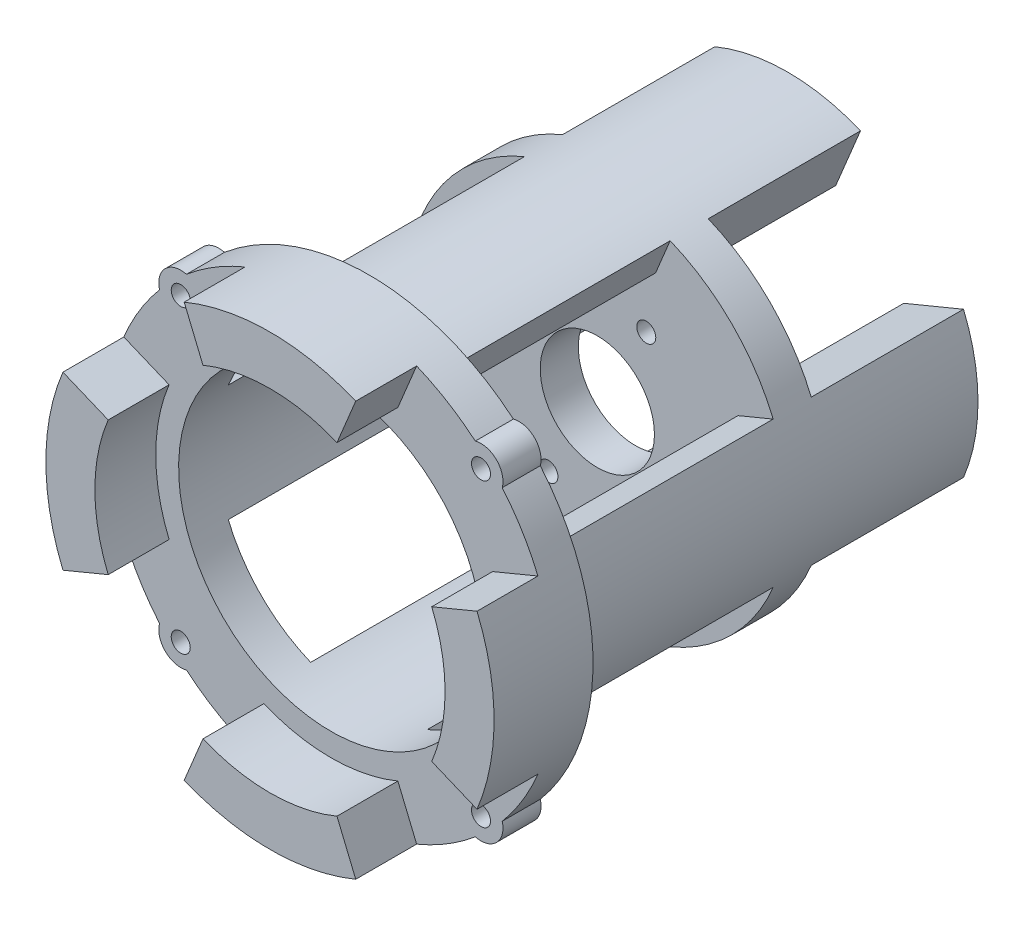
SolidWorks part; units mm, degrees
ref_plane "Front Plane" through (0, 0, 0) normal (0, 0, 1) x (1, 0, 0)
ref_plane "Top Plane" through (0, 0, 0) normal (0, 1, 0) x (1, 0, 0)
ref_plane "Right Plane" through (0, 0, 0) normal (1, 0, 0) x (0, 0, -1)
sketch "Sketch1" plane through (0, 0, 0) normal (0, 0, 1) x (1, 0, 0)
  line L1 (20, 0) -> (25, 0) construction
  line L17 (-12.85, 0) -> (-6.425, -11.1284) construction
  line L18 (-6.425, -11.1284) -> (6.425, -11.1284) construction
  line L19 (6.425, -11.1284) -> (12.85, 0) construction
  line L20 (12.85, 0) -> (6.425, 11.1284) construction
  line L21 (6.425, 11.1284) -> (-6.425, 11.1284) construction
  line L22 (-6.425, 11.1284) -> (-12.85, 0) construction
  circle A11 centre (0, 0) radius 11 construction
  circle A12 centre (0, 0) radius 12.85 construction
  circle A13 centre (0, 0) radius 20 construction
  circle A14 centre (-12.85, 0) radius 1.25
  circle A15 centre (-6.425, 11.1284) radius 1.25
  circle A16 centre (6.425, 11.1284) radius 1.25
  circle A17 centre (12.85, 0) radius 1.25
  circle A18 centre (6.425, -11.1284) radius 1.25
  circle A19 centre (-6.425, -11.1284) radius 1.25
  circle A20 centre (0, 0) radius 7.5
  circle A21 centre (0, 0) radius 25
  dimension "D3" = 40
  dimension "D7" = 22
  dimension "D8" = 25.7
  dimension "D10" = 15
  dimension "D2" = 2.5
  dimension "D4" = 5
extrude "Boss-Extrude1" add sketch "Sketch1" along normal blind 5
sketch "Sketch2" plane through (0, 0, 0) normal (0, 0, -1) x (-1, 0, 0)
  line L0 (23.097, 9.5671) -> (15.244, 6.3143)
  line L1 (0, 0) -> (0, 25) construction
  line L2 (0, 0) -> (-9.5671, 23.097) construction
  line L3 (-9.5671, 23.097) -> (9.5671, 23.097) construction
  line L4 (9.5671, 23.097) -> (0, 0) construction
  line L5 (-9.5671, 23.097) -> (-6.3143, 15.244)
  line L6 (9.5671, 23.097) -> (6.3143, 15.244)
  line L15 (23.097, -9.5671) -> (15.244, -6.3143)
  line L16 (9.5671, -23.097) -> (6.3143, -15.244)
  line L17 (-9.5671, -23.097) -> (-6.3143, -15.244)
  line L18 (-23.097, -9.5671) -> (-15.244, -6.3143)
  line L19 (-23.097, 9.5671) -> (-15.244, 6.3143)
  circle A0 centre (0, 0) radius 16.5 construction
  circle A1 centre (0, 0) radius 25 construction
  arc A3 (-6.3143, 15.244) -> (6.3143, 15.244) centre (0, 0) cw
  circle A12 centre (0, 0) radius 25 construction
  arc A13 (-9.5671, 23.097) -> (9.5671, 23.097) centre (0, 0) cw
  arc A14 (23.097, 9.5671) -> (23.097, -9.5671) centre (0, 0) cw
  arc A15 (15.244, 6.3143) -> (15.244, -6.3143) centre (0, 0) cw
  arc A16 (9.5671, -23.097) -> (-9.5671, -23.097) centre (0, 0) cw
  arc A17 (6.3143, -15.244) -> (-6.3143, -15.244) centre (0, 0) cw
  arc A18 (-23.097, -9.5671) -> (-23.097, 9.5671) centre (0, 0) cw
  arc A19 (-15.244, -6.3143) -> (-15.244, 6.3143) centre (0, 0) cw
  point P6 (0, 23.097)
  circle M13 centre (0, 0) radius 25
  dimension "D1" = 33
  dimension "D3" = 45
extrude "Boss-Extrude2" add sketch "Sketch2" along normal blind 20 contours L18 A19 L19 M13 | L5 A3 L6 M13 | L0 A15 L15 M13 | L16 A17 L17 M13
sketch "Sketch3" plane through (0, 0, 5) normal (0, 0, 1) x (1, 0, 0)
  line L0 (9.5671, 23.097) -> (7.6537, 18.4776)
  line L1 (9.5671, 23.097) -> (6.3143, 15.244) construction
  line L2 (-9.5671, 23.097) -> (-7.6537, 18.4776)
  line L3 (-9.5671, 23.097) -> (-6.3143, 15.244) construction
  line L4 (0, 0) -> (9.5671, 23.097) construction
  line L5 (23.097, 9.5671) -> (18.4776, 7.6537)
  line L6 (23.097, -9.5671) -> (18.4776, -7.6537)
  line L7 (9.5671, -23.097) -> (7.6537, -18.4776)
  line L8 (-9.5671, -23.097) -> (-7.6537, -18.4776)
  line L9 (-23.097, -9.5671) -> (-18.4776, -7.6537)
  line L10 (-23.097, 9.5671) -> (-18.4776, 7.6537)
  circle A0 centre (0, 0) radius 20 construction
  arc A1 (-7.6537, 18.4776) -> (7.6537, 18.4776) centre (0, 0) cw
  arc A2 (-9.5671, 23.097) -> (9.5671, 23.097) centre (0, 0) cw
  arc A3 (23.097, 9.5671) -> (23.097, -9.5671) centre (0, 0) cw
  arc A4 (18.4776, 7.6537) -> (18.4776, -7.6537) centre (0, 0) cw
  arc A5 (9.5671, -23.097) -> (-9.5671, -23.097) centre (0, 0) cw
  arc A6 (7.6537, -18.4776) -> (-7.6537, -18.4776) centre (0, 0) cw
  arc A7 (-23.097, -9.5671) -> (-23.097, 9.5671) centre (0, 0) cw
  arc A8 (-18.4776, -7.6537) -> (-18.4776, 7.6537) centre (0, 0) cw
  circle M8 centre (0, 0) radius 25
extrude "Boss-Extrude3" add sketch "Sketch3" along normal blind 30 contours L2 A1 L0 M8 | L5 A4 L6 M8 | L7 A6 L8 M8 | L9 A8 L10 M8
sketch "Sketch4" plane through (0, 0, 35) normal (0, 0, 1) x (1, 0, 0)
  line L0 (0, 0) -> (-20.8147, 20.8147) construction
  line L1 (-17.6777, 17.6777) -> (-16.9305, 20.4661) construction
  line L2 (-16.9305, 20.4661) -> (-18.9718, 22.5073) construction
  line L3 (-18.9718, 22.5073) -> (-21.7602, 21.7602) construction
  line L4 (-21.7602, 21.7602) -> (-22.5073, 18.9718) construction
  line L5 (-22.5073, 18.9718) -> (-20.4661, 16.9305) construction
  line L6 (-20.4661, 16.9305) -> (-17.6777, 17.6777) construction
  line L7 (0, 0) -> (0, 29.4365) construction
  circle A0 centre (0, 0) radius 25 construction
  circle A1 centre (0, 0) radius 20
  arc A2 (7.6537, 18.4776) -> (-7.6537, 18.4776) centre (0, 0) ccw construction
  arc A3 (9.5671, 23.097) -> (-9.5671, 23.097) centre (0, 0) ccw construction
  circle A4 centre (-19.7189, 19.7189) radius 2.5 construction
  circle A5 centre (0, 0) radius 29.4365
  arc A6 (-22.5073, 18.9718) -> (-18.9718, 22.5073) centre (-19.7189, 19.7189) cw
  circle A7 centre (-19.7189, 19.7189) radius 1.25
  arc A8 (18.9718, 22.5073) -> (22.5073, 18.9718) centre (19.7189, 19.7189) cw
  circle A9 centre (19.7189, 19.7189) radius 1.25
  arc A10 (22.5073, -18.9718) -> (18.9718, -22.5073) centre (19.7189, -19.7189) cw
  circle A11 centre (19.7189, -19.7189) radius 1.25
  arc A12 (-18.9718, -22.5073) -> (-22.5073, -18.9718) centre (-19.7189, -19.7189) cw
  circle A13 centre (-19.7189, -19.7189) radius 1.25
  point P20 (-22.5073, -18.9718)
  point P23 (-18.9718, -22.5073)
  dimension "D2" = 2.5
  dimension "D1" = 5
  dimension "D3" = 45
extrude "Boss-Extrude4" add sketch "Sketch4" along normal blind 5
sketch "Sketch5" plane through (0, 0, 40) normal (0, 0, 1) x (1, 0, 0)
  line L0 (-20, 0) -> (-23, 0) construction
  line L1 (0, 0) -> (0, 29.4365) construction
  line L2 (0, 0) -> (-11.2649, 27.1958) construction
  line L3 (-11.2649, 27.1958) -> (11.2649, 27.1958) construction
  line L4 (11.2649, 27.1958) -> (0, 0) construction
  line L6 (-11.2649, 27.1958) -> (-8.8017, 21.2492)
  line L7 (11.2649, 27.1958) -> (8.8017, 21.2492)
  line L8 (27.1958, -11.2649) -> (21.2492, -8.8017)
  line L9 (27.1958, 11.2649) -> (21.2492, 8.8017)
  line L10 (-11.2649, -27.1958) -> (-8.8017, -21.2492)
  line L11 (11.2649, -27.1958) -> (8.8017, -21.2492)
  line L12 (-27.1958, 11.2649) -> (-21.2492, 8.8017)
  line L13 (-27.1958, -11.2649) -> (-21.2492, -8.8017)
  circle A0 centre (0, 0) radius 20 construction
  arc A1 (-18.4776, 7.6537) -> (-18.4776, -7.6537) centre (0, 0) ccw construction
  circle A2 centre (0, 0) radius 29.4365 construction
  arc A3 (-22.5073, 18.9718) -> (-22.5073, -18.9718) centre (0, 0) ccw construction
  circle A4 centre (0, 0) radius 23 construction
  arc A5 (-8.8017, 21.2492) -> (8.8017, 21.2492) centre (0, 0) cw
  arc A6 (-11.2649, 27.1958) -> (11.2649, 27.1958) centre (0, 0) cw
  arc A7 (27.1958, 11.2649) -> (27.1958, -11.2649) centre (0, 0) cw
  arc A8 (21.2492, 8.8017) -> (21.2492, -8.8017) centre (0, 0) cw
  arc A9 (11.2649, -27.1958) -> (-11.2649, -27.1958) centre (0, 0) cw
  arc A10 (8.8017, -21.2492) -> (-8.8017, -21.2492) centre (0, 0) cw
  arc A11 (-27.1958, -11.2649) -> (-27.1958, 11.2649) centre (0, 0) cw
  arc A12 (-21.2492, -8.8017) -> (-21.2492, 8.8017) centre (0, 0) cw
  point P13 (0, 27.1958)
  dimension "D1" = 3
  dimension "D3" = 45
extrude "Boss-Extrude5" add sketch "Sketch5" along normal blind 8
